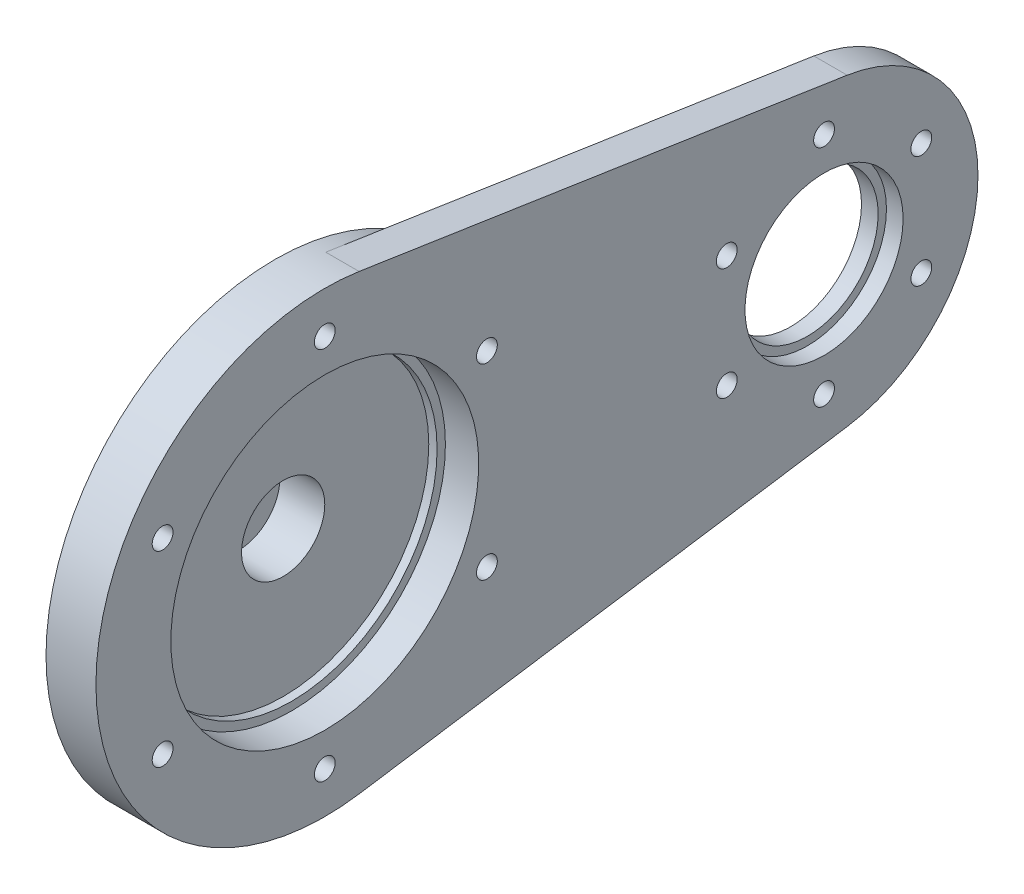
SolidWorks part; units mm, degrees
material "7075-T6 (SN)"
ref_plane "정면" through (0, 0, 0) normal (0, 0, 1) x (1, 0, 0)
ref_plane "윗면" through (0, 0, 0) normal (0, 1, 0) x (1, 0, 0)
ref_plane "우측면" through (0, 0, 0) normal (1, 0, 0) x (0, 0, -1)
sketch "스케치3" plane through (0, 0, 0) normal (1, 0, 0) x (0, 0, -1)
  circle A0 centre (0, 0) radius 27.5
  dimension "D1" = 55
extrude "보스-돌출1" add sketch "스케치3" along normal blind 2
sketch "스케치4" plane through (2, 0, 0) normal (1, 0, 0) x (0, 0, -1)
  circle A0 centre (0, 0) radius 17.5
  circle A1 centre (0, 0) radius 27.5
  circle A2 centre (0, 0) radius 27.5 construction
  dimension "D1" = 35
extrude "보스-돌출2" add sketch "스케치4" along normal blind 1
sketch "스케치5" plane through (3, 0, 0) normal (1, 0, 0) x (0, 0, -1)
  circle A0 centre (0, 0) radius 18.5
  circle A1 centre (0, 0) radius 27.5
  circle A2 centre (0, 0) radius 27.5 construction
  dimension "D1" = 37
extrude "보스-돌출3" add sketch "스케치5" along normal blind 7
sketch "스케치6" plane through (10, 0, 0) normal (1, 0, 0) x (0, 0, -1)
  circle A0 centre (0, 0) radius 27.5
  circle A1 centre (0, 0) radius 17.5
  circle A2 centre (0, 0) radius 27.5 construction
  dimension "D1" = 35
extrude "보스-돌출4" add sketch "스케치6" along normal blind 2
sketch "스케치10" plane through (12, 0, 0) normal (1, 0, 0) x (0, 0, -1)
  line L0 (0, 0) -> (60, 0) construction
  line L1 (4.125, 27.1889) -> (62.775, 18.2907)
  line L2 (4.125, -27.1889) -> (62.775, -18.2907)
  arc A0 (62.775, -18.2907) -> (62.775, 18.2907) centre (60, 0) ccw
  arc A1 (4.125, -27.1889) -> (4.125, 27.1889) centre (0, 0) ccw
  circle A2 centre (0, 0) radius 27.5 construction
  dimension "D1" = 37
  dimension "D2" = 60
extrude "보스-돌출5" add sketch "스케치10" against normal blind 9
ref_plane "평면2" through (7.5, 0, 0) normal (1, 0, 0) x (0, 0, -1)
sketch "스케치11" plane through (7.5, 0, 0) normal (1, 0, 0) x (0, 0, -1)
  circle A0 centre (60, 0) radius 8.5
  arc A1 (62.775, -18.2907) -> (62.775, 18.2907) centre (60, 0) ccw construction
  dimension "D1" = 17
extrude "컷-돌출3" cut sketch "스케치11" against normal mid plane 222
sketch "스케치12" plane through (7.5, 0, 0) normal (1, 0, 0) x (0, 0, -1)
  circle A0 centre (60, 0) radius 9.5
  circle A1 centre (60, 0) radius 8.5 construction
  dimension "D1" = 19
extrude "컷-돌출4" cut sketch "스케치12" against normal mid plane 5
sketch "스케치13" plane through (0, 0, 0) normal (-1, 0, 0) x (0, 0, 1)
  circle A0 centre (0, 0) radius 9.5
  circle A1 centre (0, 0) radius 27.5 construction
  dimension "D1" = 19
extrude "보스-돌출6" add sketch "스케치13" along normal blind 5
sketch "스케치14" plane through (2, 0, 0) normal (1, 0, 0) x (0, 0, -1)
  circle A0 centre (0, 0) radius 5 construction
  dimension "D1" = 10
hole_wizard "M3 육각 소켓 머리 캡 나사용 카운터보어1" [suppressed] positions "스케치15" profile "스케치16" counterbore size "M3" standard "ISO"
sketch "스케치15" plane through (2, 0, 0) normal (1, 0, 0) x (0, 0, -1)
  circle A0 centre (0, 0) radius 5 construction
  point P0 (0, 5)
sketch "스케치16" plane through (2, 5, 0) normal (0, 1, 0) x (0, 0, -1)
  line L0 (0, 0) -> (0, 7)
  line L1 (0, 7) -> (1.7, 7)
  line L3 (1.7, 7) -> (1.7, 3.4)
  line L4 (1.7, 3.4) -> (3.25, 3.4)
  line L5 (3.25, 3.4) -> (3.25, 0)
  line L7 (3.25, 0) -> (0, 0)
  line L11 (0, -6.35) -> (0, 107.95) construction
  dimension "관통 구멍 지름" = 3.4
  dimension "관통 구멍 깊이" = 7
  dimension "카운터보어 지름" = 6.5
  dimension "카운터보어 깊이" = 3.4
pattern_circular "원형 패턴1" [suppressed] count 3 over 360
sketch "스케치17" plane through (0, 0, 0) normal (0, 0, 1) x (1, 0, 0)
  line L0 (12, -27.5) -> (12, 27.5) construction
  line L1 (7, 30.4497) -> (24.7141, 30.4497)
  line L2 (7, 30.4497) -> (7, -34.1546)
  line L3 (7, -34.1546) -> (24.7141, -34.1546)
  line L4 (24.7141, 30.4497) -> (24.7141, -34.1546)
  dimension "D1" = 5
extrude "컷-돌출5" cut sketch "스케치17" against normal mid plane 2222
sketch "스케치18" plane through (7, 0, 0) normal (1, 0, 0) x (0, 0, -1)
  circle A0 centre (0, 0) radius 22.5 construction
  circle A1 centre (0, 0) radius 17.5 construction
  dimension "D1" = 45
hole_wizard "M3 탭을 위한 탭 드릴1" positions "스케치19" profile "스케치20" hole size "M3" standard "ISO" end condition through all
sketch "스케치19" plane through (7, 0, 0) normal (1, 0, 0) x (0, 0, -1)
  circle A0 centre (0, 0) radius 22.5 construction
  point P0 (0, 22.5)
sketch "스케치20" plane through (7, 22.5, 0) normal (0, 1, 0) x (0, 0, -1)
  line L0 (0, 0) -> (0, 12)
  line L1 (0, 12) -> (1.25, 12)
  line L2 (1.25, 12) -> (1.25, 0)
  line L5 (1.25, 0) -> (0, 0)
  line L11 (0, -6.35) -> (0, 107.95) construction
  dimension "관통 구멍 지름" = 2.5
  dimension "관통 구멍 깊이" = 12
pattern_circular "원형 패턴2" count 6 over 360 about axis through (0, 0, 0) along (1, 0, 0) of "M3 탭을 위한 탭 드릴1"
sketch "스케치21" plane through (7, 0, 0) normal (1, 0, 0) x (0, 0, -1)
  circle A0 centre (60, 0) radius 13.5 construction
  circle A1 centre (60, 0) radius 8.5 construction
  dimension "D1" = 27
hole_wizard "M3 탭을 위한 탭 드릴2" positions "스케치24" profile "스케치25" hole size "M3" standard "ISO" end condition through all
sketch "스케치24" plane through (7, 0, 0) normal (1, 0, 0) x (0, 0, -1)
  circle A0 centre (60, 0) radius 13.5 construction
  point P0 (60, 13.5)
sketch "스케치25" plane through (7, 13.5, -60) normal (0, 1, 0) x (0, 0, -1)
  line L0 (0, 0) -> (0, 12)
  line L1 (0, 12) -> (1.25, 12)
  line L2 (1.25, 12) -> (1.25, 0)
  line L5 (1.25, 0) -> (0, 0)
  line L11 (0, -6.35) -> (0, 107.95) construction
  dimension "관통 구멍 지름" = 2.5
  dimension "관통 구멍 깊이" = 12
pattern_circular "원형 패턴3" count 6 over 360 about axis through (0, 0, -60) along (1, 0, 0) of "M3 탭을 위한 탭 드릴2"
sketch "스케치26" plane through (0, 0, 0) normal (-1, 0, 0) x (0, 0, 1)
  circle A0 centre (0, 0) radius 25
  circle A1 centre (0, 0) radius 27.5 construction
  circle A2 centre (0, 0) radius 27.5
  dimension "D1" = 50
extrude "컷-돌출6" cut sketch "스케치26" against normal blind 1
fillet "필렛1" radius 0.1 2 edges at (0, 0, 9.5) (-5, 0, 9.5)
sketch "스케치27" plane through (-5, 0, 0) normal (-1, 0, 0) x (0, 0, 1)
  circle A0 centre (0, 0) radius 7 construction
  circle A1 centre (0, 0) radius 9.4 construction
  dimension "D1" = 14
hole_wizard "Ø3.0mm 맞춤핀 구멍1" positions "스케치28" profile "스케치29" hole size "Ø3.0" standard "ISO"
sketch "스케치28" plane through (-5, 0, 0) normal (-1, 0, 0) x (0, 0, 1)
  circle A0 centre (0, 0) radius 7 construction
  point P0 (0, -7)
sketch "스케치29" plane through (-5, -7, 0) normal (0, 1, 0) x (0, 0, 1)
  line L0 (0, 0) -> (0, 5.9013)
  line L1 (0, 5.9013) -> (1.5, 5)
  line L2 (1.5, 5) -> (1.5, 0)
  line L5 (1.5, 0) -> (0, 0)
  line L10 (0, 5.9013) -> (-1.5, 5) construction
  line L11 (0, -6.35) -> (0, 107.95) construction
  dimension "구멍 지름" = 3
  dimension "구멍 깊이" = 5
  dimension "드릴 각도" = 118
pattern_circular "원형 패턴4" count 3 over 360 about axis through (0, 0, 0) along (1, 0, 0) of "Ø3.0mm 맞춤핀 구멍1"
hole_wizard "M5 육각 소켓 머리 캡 나사용 카운터보어1" positions "스케치36" profile "스케치37" counterbore size "M5" standard "ISO" end condition through all
sketch "스케치36" plane through (2, 0, 0) normal (1, 0, 0) x (0, 0, -1)
  point P0 (0, 0)
sketch "스케치37" plane through (2, 0, 0) normal (0, 1, 0) x (0, 0, -1)
  line L0 (0, 0) -> (0, 7)
  line L1 (0, 7) -> (2.65, 7)
  line L3 (2.65, 7) -> (2.65, 5.4)
  line L4 (2.65, 5.4) -> (5, 5.4)
  line L5 (5, 5.4) -> (5, 0)
  line L7 (5, 0) -> (0, 0)
  line L11 (0, -6.35) -> (0, 107.95) construction
  dimension "관통 구멍 지름" = 5.3
  dimension "관통 구멍 깊이" = 7
  dimension "카운터보어 지름" = 10
  dimension "카운터보어 깊이" = 5.4
